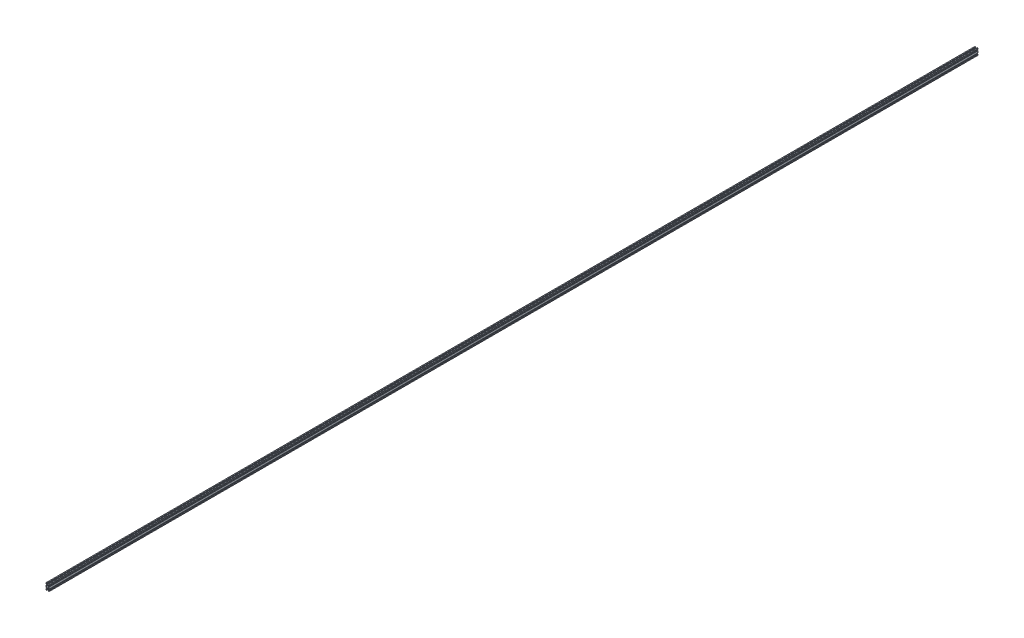
SolidWorks part; units mm, degrees
ref_plane "Front Plane" through (0, 0, 0) normal (0, 0, 1) x (1, 0, 0)
ref_plane "Top Plane" through (0, 0, 0) normal (0, 1, 0) x (1, 0, 0)
ref_plane "Right Plane" through (0, 0, 0) normal (1, 0, 0) x (0, 0, -1)
sketch "Sketch1" plane through (0, 0, 0) normal (0, 0, 1) x (1, 0, 0)
  line L68 (-4, -18.5) -> (-4, -20)
  line L69 (4, -20) -> (4, -18.5)
  line L70 (8.5, -14) -> (10, -14)
  line L71 (10, -6) -> (8.5, -6)
  line L72 (8.5, 6) -> (10, 6)
  line L73 (10, 14) -> (8.5, 14)
  line L74 (4, 18.5) -> (4, 20)
  line L75 (-4, 20) -> (-4, 18.5)
  line L76 (-8.5, 14) -> (-10, 14)
  line L77 (-10, 6) -> (-8.5, 6)
  line L78 (-8.5, -6) -> (-10, -6)
  line L79 (-10, -14) -> (-8.5, -14)
  line L80 (-3.9393, -5) -> (-1.5601, -2.6208)
  line L81 (-2.6208, -1.5601) -> (-5, -3.9393)
  line L82 (-5, -3.9393) -> (-8.9393, 0)
  line L83 (-8.9393, 0) -> (-5, 3.9393)
  line L84 (-5, 3.9393) -> (-2.6208, 1.5601)
  line L85 (-1.5601, 2.6208) -> (-3.9393, 5)
  line L86 (-3.9393, 5) -> (-1.5601, 7.3792)
  line L87 (1.5601, 7.3792) -> (3.9393, 5)
  line L88 (3.9393, 5) -> (1.5601, 2.6208)
  line L89 (2.6208, 1.5601) -> (5, 3.9393)
  line L90 (5, 3.9393) -> (8.9393, 0)
  line L91 (8.9393, 0) -> (5, -3.9393)
  line L92 (5, -3.9393) -> (2.6208, -1.5601)
  line L93 (1.5601, -2.6208) -> (3.9393, -5)
  line L94 (3.9393, -5) -> (1.5601, -7.3792)
  line L95 (-1.5601, -7.3792) -> (-3.9393, -5)
  line L96 (-10, -14) -> (-10, -20)
  line L97 (-10, -20) -> (-4, -20)
  line L98 (-4, -18.5) -> (-7.5272, -18.5)
  line L99 (-7.5272, -18.5) -> (-3.0272, -14)
  line L100 (-3.0272, -14) -> (3.0272, -14)
  line L101 (3.0272, -14) -> (7.5272, -18.5)
  line L102 (7.5272, -18.5) -> (4, -18.5)
  line L103 (4, -20) -> (10, -20)
  line L104 (10, -20) -> (10, -14)
  line L105 (8.5, -14) -> (8.5, -17.5272)
  line L106 (8.5, -17.5272) -> (4, -13.0272)
  line L107 (4, -13.0272) -> (4, -6.9728)
  line L108 (4, -6.9728) -> (8.5, -2.4728)
  line L109 (8.5, -2.4728) -> (8.5, -6)
  line L110 (10, -6) -> (10, 6)
  line L111 (8.5, 6) -> (8.5, 2.4728)
  line L112 (8.5, 2.4728) -> (4, 6.9728)
  line L113 (4, 6.9728) -> (4, 13.0272)
  line L114 (4, 13.0272) -> (8.5, 17.5272)
  line L115 (8.5, 17.5272) -> (8.5, 14)
  line L116 (10, 14) -> (10, 20)
  line L117 (10, 20) -> (4, 20)
  line L118 (4, 18.5) -> (7.5272, 18.5)
  line L119 (7.5272, 18.5) -> (3.0272, 14)
  line L120 (3.0272, 14) -> (-3.0272, 14)
  line L121 (-3.0272, 14) -> (-7.5272, 18.5)
  line L122 (-7.5272, 18.5) -> (-4, 18.5)
  line L123 (-4, 20) -> (-10, 20)
  line L124 (-10, 20) -> (-10, 14)
  line L125 (-8.5, 14) -> (-8.5, 17.5272)
  line L126 (-8.5, 17.5272) -> (-4, 13.0272)
  line L127 (-4, 13.0272) -> (-4, 6.9728)
  line L128 (-4, 6.9728) -> (-8.5, 2.4728)
  line L129 (-8.5, 2.4728) -> (-8.5, 6)
  line L130 (-10, 6) -> (-10, -6)
  line L131 (-8.5, -6) -> (-8.5, -2.4728)
  line L132 (-8.5, -2.4728) -> (-4, -6.9728)
  line L133 (-4, -6.9728) -> (-4, -13.0272)
  line L134 (-4, -13.0272) -> (-8.5, -17.5272)
  line L135 (-8.5, -17.5272) -> (-8.5, -14)
  arc A6 (-2.6208, -1.5601) -> (-1.5601, -2.6208) centre (0, 0) ccw
  arc A7 (-1.5601, 2.6208) -> (-2.6208, 1.5601) centre (0, 0) ccw
  arc A8 (2.6208, 1.5601) -> (1.5601, 2.6208) centre (0, 0) ccw
  arc A9 (1.5601, -2.6208) -> (2.6208, -1.5601) centre (0, 0) ccw
  arc A10 (1.5601, 7.3792) -> (-1.5601, 7.3792) centre (0, 10) ccw
  arc A11 (-1.5601, -7.3792) -> (1.5601, -7.3792) centre (0, -10) ccw
extrude "Extrusão1" add sketch "Sketch1" along normal blind 6000
